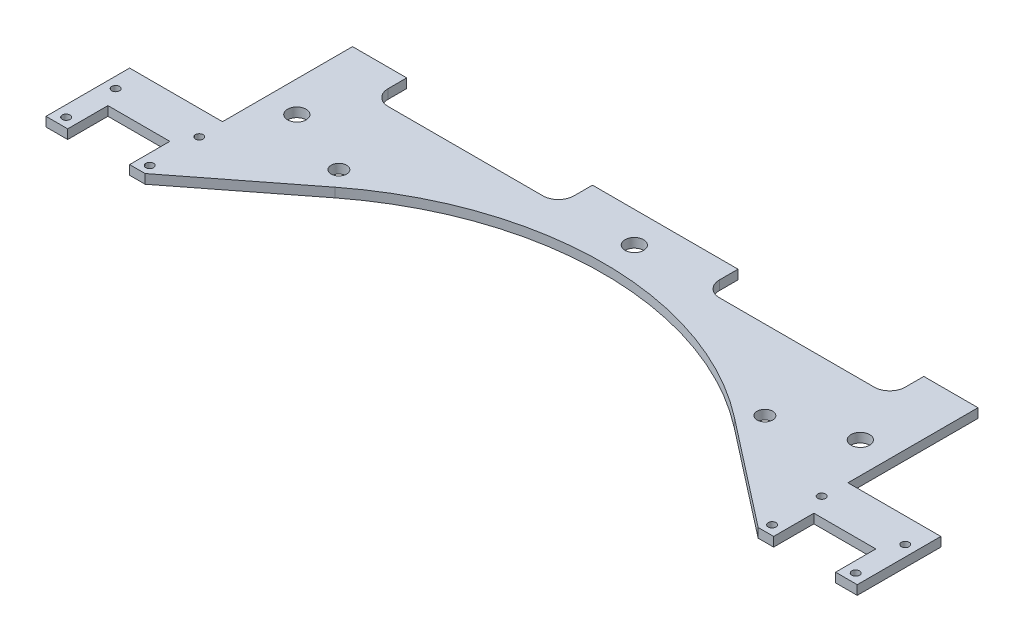
SolidWorks part; units mm, degrees
ref_plane "Face" through (0, 0, 0) normal (0, 0, 1) x (1, 0, 0)
ref_plane "Dessus" through (0, 0, 0) normal (0, 1, 0) x (1, 0, 0)
ref_plane "Droite" through (0, 0, 0) normal (1, 0, 0) x (0, 0, -1)
sketch "Esquisse1" plane through (0, 0, 0) normal (0, 1, 0) x (1, 0, 0)
  line L0 (0, 0) -> (0, 372.8366) construction
  line L1 (0, 0) -> (0, -232.7616) construction
  line L2 (558.5742, 0) -> (-497.8331, 0) construction
  line L3 (-64.4944, 52.8582) -> (-99, 26)
  line L4 (-131, 26) -> (-124, 26)
  line L5 (-131, 26) -> (-131, 53)
  line L6 (-131, 53) -> (-101, 53)
  line L7 (131, 26) -> (131, 53)
  line L8 (-131, 26) -> (-99, 26) construction
  line L9 (64.4944, 52.8582) -> (99, 26)
  line L10 (-78.5, 84) -> (-28.5, 84)
  line L11 (-83.5, 95) -> (-83.5, 89)
  line L12 (-23.5, 95) -> (-23.5, 89)
  line L13 (-23.5, 95) -> (23.5, 95)
  line L14 (-78.5, 89) -> (-28.5, 89) construction
  line L15 (83.5, 95) -> (83.5, 89)
  line L16 (101, 95) -> (83.5, 95)
  line L17 (78.5, 84) -> (28.5, 84)
  line L18 (-101, 53) -> (-101, 95)
  line L19 (-101, 95) -> (-83.5, 95)
  line L20 (-124, 26) -> (-124, 39)
  line L21 (-124, 39) -> (-104, 39)
  line L22 (-104, 39) -> (-104, 26)
  line L23 (-104, 26) -> (-99, 26)
  line L24 (-115, 26) -> (-115, 39) construction
  line L25 (131, 26) -> (124, 26)
  line L26 (124, 26) -> (124, 39)
  line L27 (124, 39) -> (104, 39)
  line L28 (104, 39) -> (104, 26)
  line L29 (104, 26) -> (99, 26)
  line L30 (131, 53) -> (101, 53)
  line L31 (101, 53) -> (101, 95)
  line L32 (-64.4944, 52.8582) -> (64.4944, 52.8582) construction
  line L33 (-64.4944, 52.8582) -> (-68.794, 58.382) construction
  line L34 (23.5, 95) -> (23.5, 89)
  line L35 (-127.5, 26) -> (-127.5, 45) construction
  line L36 (-127.5, 45) -> (-100.5, 45) construction
  line L37 (-100.5, 45) -> (-100.5, 26) construction
  line L38 (-127.5, 37) -> (-100.5, 37) construction
  line L39 (-127.5, 29) -> (-100.5, 29) construction
  arc A0 (64.4944, 52.8582) -> (-64.4944, 52.8582) centre (0, -30) ccw
  arc A1 (-83.5, 89) -> (-78.5, 84) centre (-78.5, 89) ccw
  arc A2 (-28.5, 84) -> (-23.5, 89) centre (-28.5, 89) ccw
  arc A3 (83.5, 89) -> (78.5, 84) centre (78.5, 89) cw
  arc A4 (28.5, 84) -> (23.5, 89) centre (28.5, 89) cw
  circle A5 centre (-91, 67) radius 3
  circle A6 centre (91, 67) radius 3
  circle A7 centre (-127.5, 45) radius 1.25
  circle A9 centre (-100.5, 45) radius 1.25
  circle A11 centre (-68.794, 58.382) radius 2.5
  circle A12 centre (68.794, 58.382) radius 2.5
  circle A13 centre (0, 85) radius 3
  circle A14 centre (-127.5, 29) radius 1.25
  circle A15 centre (-100.5, 29) radius 1.25
  circle A16 centre (100.5, 45) radius 1.25
  circle A18 centre (100.5, 29) radius 1.25
  circle A19 centre (127.5, 29) radius 1.25
  circle A21 centre (127.5, 45) radius 1.25
  point P3 (0, 75)
  point P21 (0, 95)
  dimension "D2" = 105
  dimension "D3" = 32
  dimension "D6" = 30
  dimension "D8" = 42
  dimension "D11" = 47.5
  dimension "D17" = 10
  dimension "D19" = 5
  dimension "D21" = 6
  dimension "D13" = 6
  dimension "D26" = 2.5
  dimension "D1" = 30
  dimension "D4" = 69
  dimension "D5" = 131
  dimension "D7" = 11
  dimension "D9" = 60
  dimension "D10" = 20
  dimension "D12" = 5
  dimension "D14" = 7
  dimension "D15" = 5
  dimension "D16" = 13
  dimension "D18" = 14
  dimension "D20" = 7
  dimension "D22" = 10
  dimension "D23" = 8
  dimension "D24" = 8
  dimension "D25" = 3
  dimension "D27" = 27
extrude "Extrusion1" add sketch "Esquisse1" along normal blind 3
